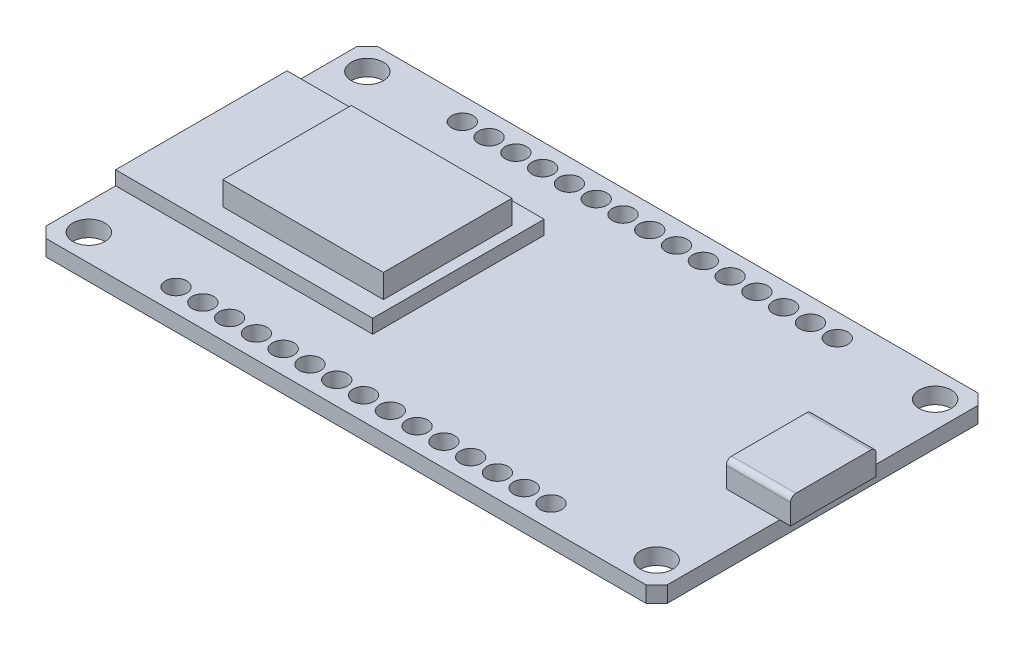
SolidWorks part; units mm, degrees
ref_plane "Front Plane" through (0, 0, 0) normal (0, 0, 1) x (1, 0, 0)
ref_plane "Top Plane" through (0, 0, 0) normal (0, 1, 0) x (1, 0, 0)
ref_plane "Right Plane" through (0, 0, 0) normal (1, 0, 0) x (0, 0, -1)
sketch "Sketch1" plane through (0, 0, 0) normal (0, 1, 0) x (1, 0, 0)
  line L0 (0, 30) -> (1, 31)
  line L1 (1, 0) -> (57, 0)
  line L2 (0, 1) -> (0, 30)
  line L3 (1, 31) -> (57, 31)
  line L4 (58, 1) -> (58, 30)
  line L5 (57, 31) -> (58, 30)
  line L6 (0, 1) -> (1, 0)
  line L7 (57, 0) -> (58, 1)
  circle A0 centre (2.5, 28.5) radius 1.5
  circle A1 centre (2.5, 2.5) radius 1.5
  circle A2 centre (55.5, 28.5) radius 1.5
  circle A3 centre (55.5, 2.5) radius 1.5
  point P0 (0, 0)
  point P1 (58, 31)
  point P2 (0, 31)
  point P3 (58, 0)
  dimension "D3" = 3
  dimension "D4" = 3
  dimension "D5" = 3
  dimension "D7" = 3
  dimension "D1" = 31
  dimension "D2" = 58
  dimension "D9" = 2.5
  dimension "D12" = 2.5
  dimension "D13" = 2.5
  dimension "D14" = 2.5
  dimension "D15" = 2.5
  dimension "D16" = 2.5
  dimension "D17" = 2.5
  dimension "D18" = 2.5
extrude "Boss-Extrude1" add sketch "Sketch1" along normal blind 1.5
sketch "Sketch2" plane through (0, 1.5, 0) normal (0, 1, 0) x (1, 0, 0)
  line L0 (0, 30) -> (0, 1) construction
  line L1 (0, 23.5) -> (24, 23.5)
  line L2 (0, 23.5) -> (0, 7.5)
  line L3 (0, 7.5) -> (24, 7.5)
  line L4 (24, 23.5) -> (24, 7.5)
  point P4 (0, 15.5)
  dimension "D1" = 16
  dimension "D2" = 24
extrude "Boss-Extrude2" add sketch "Sketch2" along normal blind 1.3
sketch "Sketch3" plane through (0, 2.8, 0) normal (0, 1, 0) x (1, 0, 0)
  line L0 (0, 7.5) -> (24, 7.5) construction
  line L1 (8, 21.5) -> (23, 21.5)
  line L2 (8, 21.5) -> (8, 9.5)
  line L3 (8, 9.5) -> (23, 9.5)
  line L4 (23, 21.5) -> (23, 9.5)
  line L5 (24, 7.5) -> (24, 23.5) construction
  dimension "D1" = 12
  dimension "D2" = 15
  dimension "D3" = 2
  dimension "D4" = 1
extrude "Boss-Extrude3" add sketch "Sketch3" along normal blind 2.2
sketch "Sketch4" plane through (0, 1.5, 0) normal (0, 1, 0) x (1, 0, 0)
  line L0 (0, 7.5) -> (0, 1) construction
  line L1 (58, 15.5) -> (0, 15.5) construction
  line L2 (58, 1) -> (58, 30) construction
  line L3 (0, 23.5) -> (0, 7.5) construction
  circle A0 centre (11, 2.1397) radius 1
  circle A1 centre (13.5, 2.1397) radius 1
  circle A2 centre (16, 2.1397) radius 1
  circle A3 centre (18.5, 2.1397) radius 1
  circle A4 centre (21, 2.1397) radius 1
  circle A5 centre (23.5, 2.1397) radius 1
  circle A6 centre (26, 2.1397) radius 1
  circle A7 centre (28.5, 2.1397) radius 1
  circle A8 centre (31, 2.1397) radius 1
  circle A9 centre (33.5, 2.1397) radius 1
  circle A10 centre (36, 2.1397) radius 1
  circle A11 centre (38.5, 2.1397) radius 1
  circle A12 centre (41, 2.1397) radius 1
  circle A13 centre (43.5, 2.1397) radius 1
  circle A14 centre (46, 2.1397) radius 1
  circle A15 centre (46, 28.8603) radius 1
  circle A16 centre (43.5, 28.8603) radius 1
  circle A17 centre (41, 28.8603) radius 1
  circle A18 centre (38.5, 28.8603) radius 1
  circle A19 centre (36, 28.8603) radius 1
  circle A20 centre (33.5, 28.8603) radius 1
  circle A21 centre (31, 28.8603) radius 1
  circle A22 centre (28.5, 28.8603) radius 1
  circle A23 centre (26, 28.8603) radius 1
  circle A24 centre (23.5, 28.8603) radius 1
  circle A25 centre (21, 28.8603) radius 1
  circle A26 centre (18.5, 28.8603) radius 1
  circle A27 centre (16, 28.8603) radius 1
  circle A28 centre (13.5, 28.8603) radius 1
  circle A29 centre (11, 28.8603) radius 1
  dimension "D1" = 2
  dimension "D3" = 11
  dimension "D2" = 15
extrude "Cut-Extrude1" cut sketch "Sketch4" against normal through all
sketch "Sketch5" plane through (0, 1.5, 0) normal (0, 1, 0) x (1, 0, 0)
  line L0 (58, 1) -> (58, 30) construction
  line L1 (53, 19.5) -> (59, 19.5)
  line L2 (53, 19.5) -> (53, 11.5)
  line L3 (53, 11.5) -> (59, 11.5)
  line L4 (59, 19.5) -> (59, 11.5)
  line L5 (57, 31) -> (1, 31) construction
  dimension "D1" = 6
  dimension "D2" = 8
  dimension "D3" = 1
  dimension "D4" = 11.5
extrude "Boss-Extrude4" add sketch "Sketch5" along normal blind 2.4
fillet "Fillet1" radius 0.5 2 edges at (56, 3.9, -19.5) (56, 3.9, -11.5)
